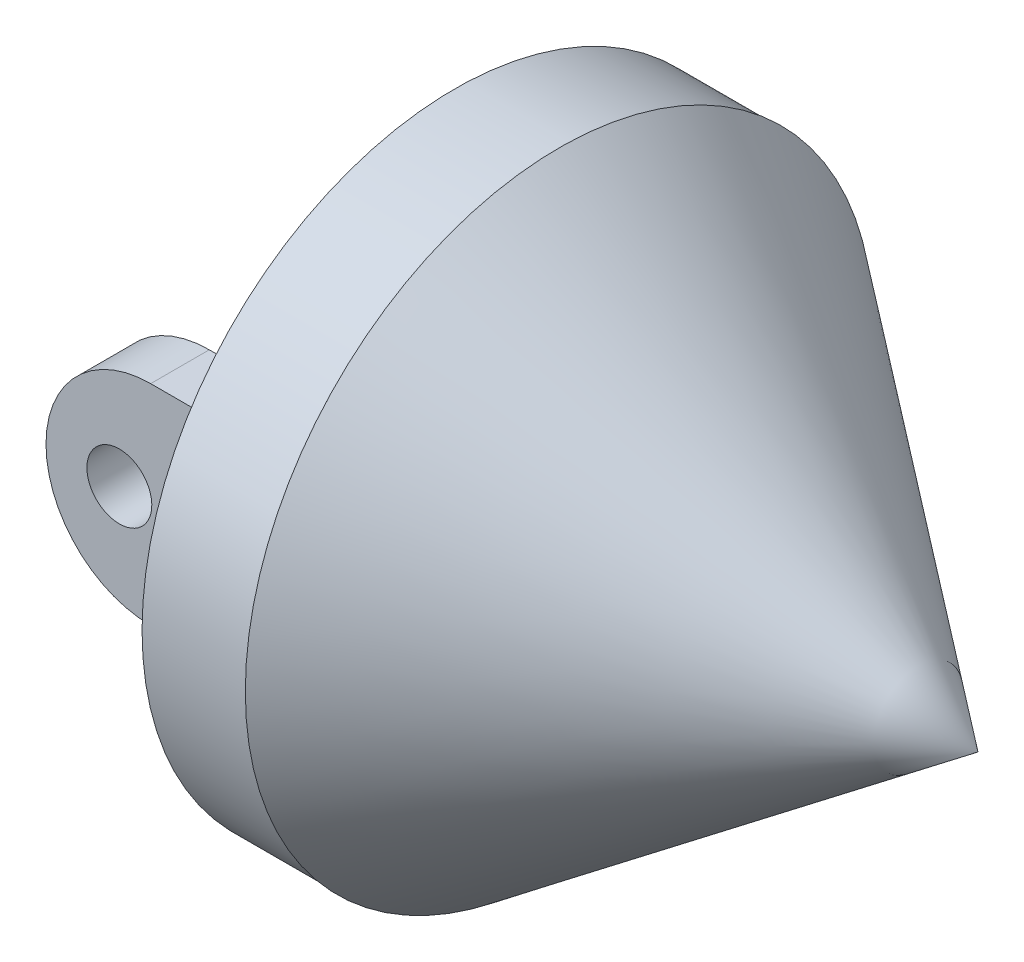
SolidWorks part; units mm, degrees
ref_plane "Front Plane" through (0, 0, 0) normal (0, 0, 1) x (1, 0, 0)
ref_plane "Top Plane" through (0, 0, 0) normal (0, 1, 0) x (1, 0, 0)
ref_plane "Right Plane" through (0, 0, 0) normal (1, 0, 0) x (0, 0, -1)
sketch "Sketch1" plane through (0, 0, 0) normal (0, 0, 1) x (1, 0, 0)
  line L0 (-31.2941, 0) -> (31.2941, 0) construction
  line L1 (0, 0) -> (0, 15)
  line L2 (0, 15) -> (20, 0)
  line L3 (0, 0) -> (20, 0)
  point P4 (0, 0)
  dimension "D1" = 20
  dimension "D2" = 15
revolve "Revolve2" add sketch "Sketch1" angle 360 about L0
sketch "Sketch3" plane through (0, 0, 0) normal (1, 0, 0) x (0, 0, -1)
  circle A0 centre (0, 0) radius 14.9335
extrude "Boss-Extrude2" add sketch "Sketch3" against normal blind 5
sketch "Sketch4" plane through (0, 0, -0.8867) normal (1, 0, 0) x (0, 0, -1)
  line L0 (23.6782, 0) -> (-23.3487, 0) construction
  line L1 (-7.6079, 7.5) -> (-11.2079, 7.5)
  line L2 (-7.6079, 7.5) -> (-7.6079, -7.5)
  line L3 (-7.6079, -7.5) -> (-11.2079, -7.5)
  line L4 (-11.2079, 7.5) -> (-11.2079, -7.5)
  line L5 (-7.6079, 7.5) -> (-11.2079, -7.5) construction
  line L6 (-7.6079, -7.5) -> (-11.2079, 7.5) construction
  point P0 (-9.4079, 0)
  point P9 (0.1648, 0)
  dimension "D1" = 15
  dimension "D2" = 3.6
extrude "Cut-Extrude1" cut sketch "Sketch4" along normal blind 2 and the other way through all from offset 0 contours L2 L1 L4 L3
sketch "Sketch5" plane through (0, 0, 0) normal (0, 0, 1) x (1, 0, 0)
  circle A0 centre (0, 0) radius 1.6
  dimension "D1" = 3.2
sketch "Sketch6" plane through (0, 0, 0) normal (1, 0, 0) x (0, 0, -1)
  line L0 (-6.7212, 7.5) -> (-6.7212, -7.5) construction
  line L1 (1.4813, 10.843) -> (-3.7212, 10.843)
  line L2 (1.4813, 10.843) -> (1.4813, -10.3338)
  line L3 (1.4813, -10.3338) -> (-3.7212, -10.3338)
  line L4 (-3.7212, 10.843) -> (-3.7212, -10.3338)
  dimension "D1" = 3
extrude "Cut-Extrude4" cut sketch "Sketch6" against normal through all from offset 4 contours L2 L1 L4 L3
sketch "Sketch8" plane through (0, 0, 0) normal (0, 0, 1) x (1, 0, 0)
  line L0 (12.8492, 0) -> (-12.8492, 0) construction
  circle A0 centre (-2.552, 6.1826) radius 1
  circle A1 centre (-2.552, -6.1826) radius 1
  point P4 (0, 0)
  dimension "D1" = 2
extrude "Cut-Extrude6" cut sketch "Sketch8" against normal blind 5
sketch "Sketch9" plane through (0, 0, 0) normal (1, 0, 0) x (0, 0, -1)
  line L0 (21.198, 0) -> (-21.198, 0)
  circle A0 centre (3.9232, 6.295) radius 1
  circle A1 centre (3.9232, -6.295) radius 1
  point P3 (0, 0)
  dimension "D1" = 2
extrude "Cut-Extrude9" cut sketch "Sketch9" against normal blind 5 contours A1 | A0
sketch "Sketch10" plane through (0, 0, 0) normal (1, 0, 0) x (0, 0, -1)
  line L1 (-6.7212, 7.5) -> (-10.3212, 7.5)
  line L2 (-6.7212, 7.5) -> (-6.7212, -7.5)
  line L3 (-6.7212, -7.5) -> (-10.3212, -7.5)
  line L4 (-10.3212, 7.5) -> (-10.3212, -7.5)
extrude "Boss-Extrude3" add sketch "Sketch10" against normal blind 15
sketch "Sketch11" plane through (0, 0, 0) normal (1, 0, 0) x (0, 0, -1)
  line L0 (-9.5212, 7.5) -> (-9.5212, -7.5)
  line L1 (-6.7212, 7.5) -> (-10.3212, 7.5)
  line L2 (-6.7212, 7.5) -> (-6.7212, -7.5)
  line L3 (-6.7212, -7.5) -> (-10.3212, -7.5)
  line L4 (-10.3212, 7.5) -> (-10.3212, -7.5)
  dimension "D1" = 2.8
extrude "Cut-Extrude10" cut sketch "Sketch11" against normal blind 12 from offset 5 contours L1 L4 L3 L0 offset against normal yes
sketch "Sketch12" plane through (0, 0, 0) normal (0, 0, 1) x (1, 0, 0)
  line L0 (-26.796, 0) -> (26.796, 0) construction
  line L2 (-15, -7.5) -> (-15, 7.5) construction
  line L3 (-10, 5) -> (-5, 5)
  line L4 (-15, 0) -> (-15, -5)
  line L5 (-15, -5) -> (-5, -5)
  line L6 (-5, 5) -> (-5, -5)
  line L7 (-5, 7.5) -> (-5, -7.5) construction
  line L8 (-22.475, 0) -> (-5, 0)
  line L9 (-15, 5) -> (-15, -5)
  line L10 (-5, 5) -> (-5, 9.2022)
  line L11 (-5, 14.9335) -> (-5, -14.9335) construction
  line L12 (-5, 9.2022) -> (-18.0105, 9.9963)
  line L13 (-18.0105, 9.9963) -> (-16.2842, -10.2699)
  line L14 (-16.2842, -10.2699) -> (-5, -9.3088)
  line L15 (-5, -9.3088) -> (-5, -5)
  arc A0 (-10, -5) -> (-10, 5) centre (-10, 0) cw
  circle A1 centre (-11.4959, 0) radius 1.55
  point P4 (0, 0)
  point P5 (0, 0)
  point P22 (-11.4959, 0)
  point P29 (0, 0)
  dimension "D3" = 5
  dimension "D4" = 3.1
  dimension "D1" = 5
  dimension "D2" = 5
extrude "Cut-Extrude11" cut sketch "Sketch12" against normal through all both and the other way through all
